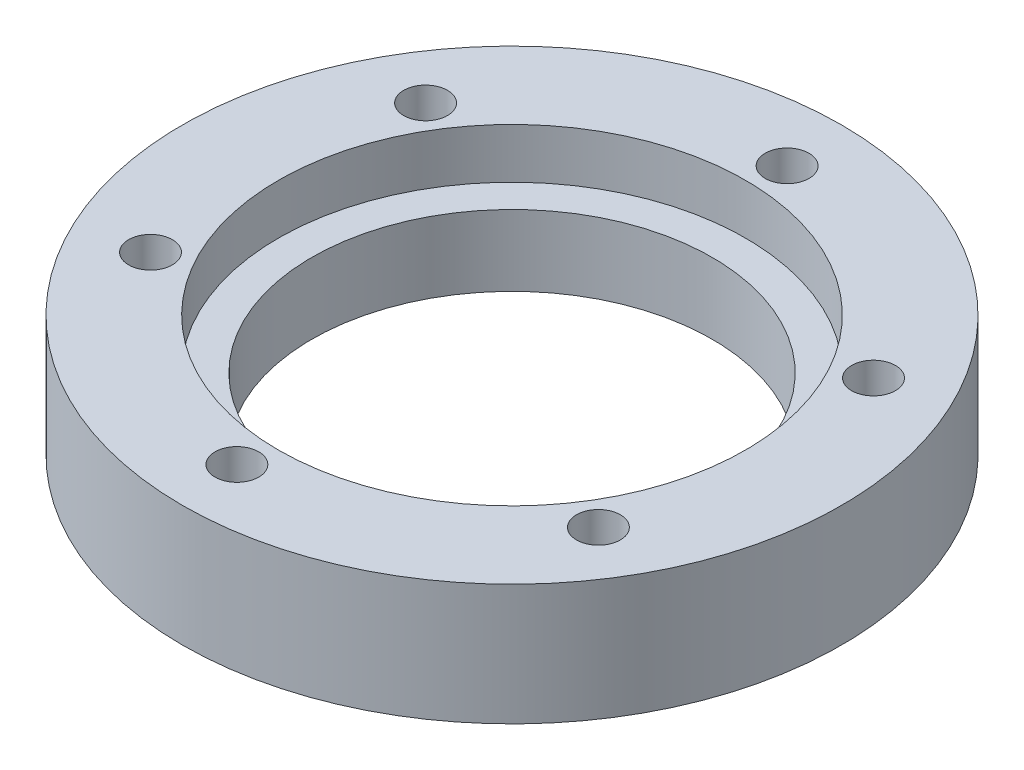
SolidWorks part; units mm, degrees
ref_plane "Front Plane" through (0, 0, 0) normal (0, 0, 1) x (1, 0, 0)
ref_plane "Top Plane" through (0, 0, 0) normal (0, 1, 0) x (1, 0, 0)
ref_plane "Right Plane" through (0, 0, 0) normal (1, 0, 0) x (0, 0, -1)
sketch "Sketch1" plane through (0, 0, 0) normal (0, 1, 0) x (1, 0, 0)
  circle A0 centre (0, 0) radius 79
extrude "Boss-Extrude1" add sketch "Sketch1" along normal blind 29
hole_wizard "CBORE for #00 Binding Head Machine Screw1" positions "Sketch2" profile "Sketch3" counterbore size "#00" standard "ANSI Inch" end condition through all
sketch "Sketch2" plane through (0, 29, 0) normal (0, 1, 0) x (1, 0, 0)
  point P0 (0, 0)
sketch "Sketch3" plane through (0, 29, 0) normal (1, 0, 0) x (0, 0, 1)
  line L0 (0, 0) -> (0, 29)
  line L1 (0, 29) -> (48, 29)
  line L3 (48, 29) -> (48, 12)
  line L4 (48, 12) -> (56, 12)
  line L5 (56, 12) -> (56, 0)
  line L7 (56, 0) -> (0, 0)
  line L11 (0, -6.35) -> (0, 107.95) construction
  dimension "Thru Hole Dia." = 96
  dimension "Thru Hole Depth" = 29
  dimension "C'Bore Dia." = 112
  dimension "C'Bore Depth" = 12
hole_wizard "Tap Drill for M12x1.5 Tap2" positions "Sketch6" profile "Sketch7" hole size "M12x1.5" standard "ANSI Metric" end condition through all
sketch "Sketch6" plane through (0, 29, 0) normal (0, 1, 0) x (1, 0, 0)
  line L1 (0, 0) -> (55.4256, -32) construction
  circle A0 centre (0, 0) radius 64 construction
  point P0 (54.411, -33.6963)
  point P22 (-1.9764, -63.9695)
  point P23 (-56.3874, -30.2732)
  point P24 (-54.411, 33.6963)
  point P25 (1.9764, 63.9695)
  point P26 (56.3874, 30.2732)
  point P27 (0, 0)
  dimension "D1" = 6
sketch "Sketch7" plane through (54.411, 29, 33.6963) normal (1, 0, 0) x (0, 0, 1)
  line L0 (0, 0) -> (0, 29)
  line L1 (0, 29) -> (5.25, 29)
  line L2 (5.25, 29) -> (5.25, 0)
  line L5 (5.25, 0) -> (0, 0)
  line L11 (0, -6.35) -> (0, 107.95) construction
  dimension "Thru Hole Dia." = 10.5
  dimension "Thru Hole Depth" = 29
